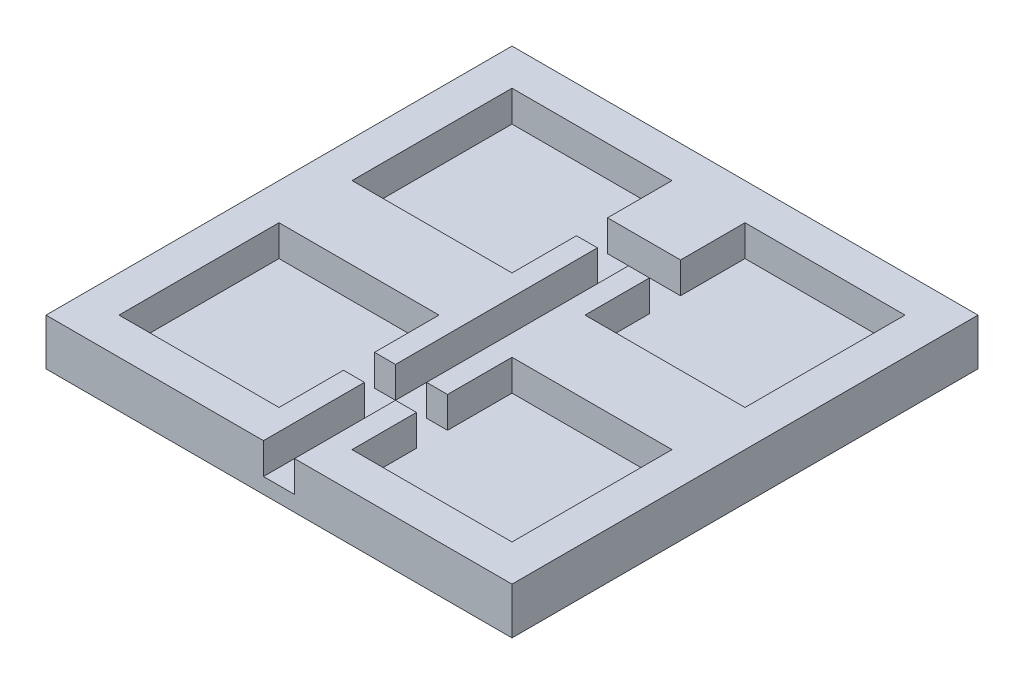
SolidWorks part; units mm, degrees
ref_plane "Front Plane" through (0, 0, 0) normal (0, 0, 1) x (1, 0, 0)
ref_plane "Top Plane" through (0, 0, 0) normal (0, 1, 0) x (1, 0, 0)
ref_plane "Right Plane" through (0, 0, 0) normal (1, 0, 0) x (0, 0, -1)
sketch "bottomSketch" plane through (0, 0, 0) normal (0, 1, 0) x (1, 0, 0)
  line L1 (15, 15) -> (-15, 15)
  line L2 (15, 15) -> (15, -15)
  line L3 (15, -15) -> (-15, -15)
  line L4 (-15, 15) -> (-15, -15)
  line L5 (15, 15) -> (-15, -15) construction
  line L6 (15, -15) -> (-15, 15) construction
  point P0 (0, 0)
  point P6 (0, 0)
  point P7 (0, 0)
  dimension "D1" = 30
extrude "bottomExtrusion" add sketch "bottomSketch" along normal blind 3
sketch "holeSketch" plane through (0, 3, 0) normal (0, 1, 0) x (1, 0, 0)
  line L0 (-15, 15) -> (-7.5, 7.5) construction
  line L1 (-15, 15) -> (-15, -15) construction
  line L2 (-15, -15) -> (-7.5, -7.5) construction
  line L3 (15, 15) -> (7.5, 7.5) construction
  line L4 (15, -15) -> (7.5, -7.5) construction
  line L5 (-15, -15) -> (15, -15) construction
  line L6 (15, -15) -> (15, 15) construction
  line L7 (-7.5, 7.5) -> (-15, 7.5) construction
  line L9 (-2.35, 2.35) -> (-12.65, 2.35)
  line L10 (-2.35, 2.35) -> (-2.35, 12.65)
  line L11 (-2.35, 12.65) -> (-12.65, 12.65)
  line L12 (-12.65, 2.35) -> (-12.65, 12.65)
  line L13 (-2.35, 2.35) -> (-12.65, 12.65) construction
  line L14 (-2.35, 12.65) -> (-12.65, 2.35) construction
  line L15 (-2.35, -12.65) -> (-12.65, -12.65)
  line L16 (-2.35, -12.65) -> (-2.35, -2.35)
  line L17 (-2.35, -2.35) -> (-12.65, -2.35)
  line L18 (-12.65, -12.65) -> (-12.65, -2.35)
  line L19 (-2.35, -12.65) -> (-12.65, -2.35) construction
  line L20 (-2.35, -2.35) -> (-12.65, -12.65) construction
  line L21 (12.65, 2.35) -> (2.35, 2.35)
  line L22 (12.65, 2.35) -> (12.65, 12.65)
  line L23 (12.65, 12.65) -> (2.35, 12.65)
  line L24 (2.35, 2.35) -> (2.35, 12.65)
  line L25 (12.65, 2.35) -> (2.35, 12.65) construction
  line L26 (12.65, 12.65) -> (2.35, 2.35) construction
  line L27 (12.65, -12.65) -> (2.35, -12.65)
  line L28 (12.65, -12.65) -> (12.65, -2.35)
  line L29 (12.65, -2.35) -> (2.35, -2.35)
  line L30 (2.35, -12.65) -> (2.35, -2.35)
  line L31 (12.65, -12.65) -> (2.35, -2.35) construction
  line L32 (12.65, -2.35) -> (2.35, -12.65) construction
  dimension "D2" = 45
  dimension "D3" = 45
  dimension "D4" = 45
  dimension "D1" = 45
  dimension "D5" = 7.5
  dimension "D6" = 10.3
extrude "holeExtrusion" cut sketch "holeSketch" against normal blind 2
sketch "lateralWireSketch" plane through (0, 3, 0) normal (0, 1, 0) x (1, 0, 0)
  line L0 (-2.35, -12.65) -> (-2.35, -2.35) construction
  line L1 (2.35, -6.5) -> (-2.35, -6.5)
  line L2 (2.35, -6.5) -> (2.35, -8.5)
  line L3 (2.35, -8.5) -> (-2.35, -8.5)
  line L4 (-2.35, -6.5) -> (-2.35, -8.5)
  line L5 (0, -8.5) -> (0, -6.5) construction
  line L6 (2.35, -7.5) -> (-2.35, -7.5) construction
  line L7 (2.35, -2.35) -> (2.35, -12.65) construction
  line L8 (2.35, 12.65) -> (2.35, 2.35) construction
  line L9 (-2.35, 8.5) -> (2.35, 8.5)
  line L10 (-2.35, 8.5) -> (-2.35, 6.5)
  line L11 (-2.35, 6.5) -> (2.35, 6.5)
  line L12 (2.35, 8.5) -> (2.35, 6.5)
  line L13 (0, 6.5) -> (0, 8.5) construction
  line L14 (-2.35, 7.5) -> (2.35, 7.5) construction
  line L15 (-2.35, 2.35) -> (-2.35, 12.65) construction
  point P0 (0, -7.5)
  point P13 (0, 7.5)
  dimension "D1" = 2
extrude "lateralWireExtrusion" cut sketch "lateralWireSketch" against normal blind 2
sketch "wireResevoirSketch" plane through (0, 3, 0) normal (0, 1, 0) x (1, 0, 0)
  line L1 (-1, 6.5) -> (1, 6.5)
  line L2 (-1, 6.5) -> (-1, -15)
  line L3 (-1, -15) -> (1, -15)
  line L4 (1, 6.5) -> (1, -15)
  line L5 (0, -15) -> (0, 6.5) construction
  line L7 (-2.35, 6.5) -> (2.35, 6.5) construction
  line L8 (-15, -15) -> (15, -15) construction
  dimension "D1" = 2
extrude "wireReservoirExtrusion" cut sketch "wireResevoirSketch" against normal blind 2
equation "\"topSize\"=25"
equation "\"D1@bottomSketch\" = \"bottom\""
equation "\"bottomExtra\"=5"
equation "\"bottom\"=\"topSize\"+\"bottomExtra\""
equation "\"D5@holeSketch\" = \"bottomExtra\" / 2 + \"notchSize\" / 2"
equation "\"notchSize\"=10"
equation "\"notchHolderSize\"=\"notchSize\"+0.3"
equation "\"D6@holeSketch\" = \"notchHolderSize\""
equation "\"notchHolderHeight\"=\"notchHeight\""
equation "\"notchHeight\"=2"
equation "\"D1@holeExtrusion\" = \"notchHolderHeight\""
equation "\"D1@lateralWireExtrusion\" = \"notchHeight\""
equation "\"D1@wireReservoirExtrusion\" = \"notchHeight\""
